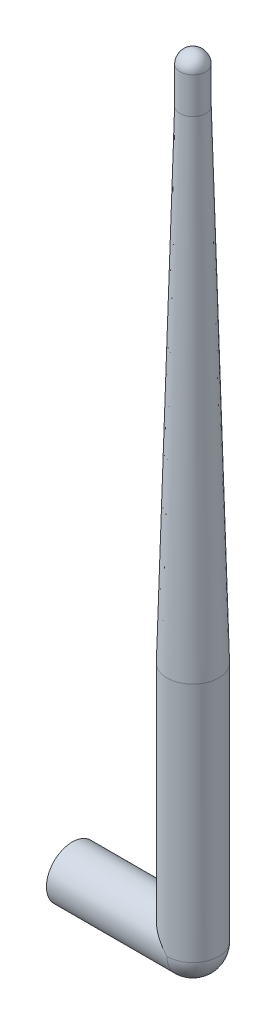
SolidWorks part; units mm, degrees
material "Rubber"
ref_plane "Front Plane" through (0, 0, 0) normal (0, 0, 1) x (1, 0, 0)
ref_plane "Top Plane" through (0, 0, 0) normal (0, 1, 0) x (1, 0, 0)
ref_plane "Right Plane" through (0, 0, 0) normal (1, 0, 0) x (0, 0, -1)
sketch "Sketch1" plane through (0, 0, 0) normal (1, 0, 0) x (0, 0, -1)
  circle A0 centre (0, 0) radius 5.461
  dimension "D1" = 10.922
extrude "Boss-Extrude1" add sketch "Sketch1" along normal blind 25.4
sketch "Sketch2" plane through (0, 0, 0) normal (-1, 0, 0) x (0, 0, 1)
  circle A0 centre (0, 0) radius 4.191
  dimension "D1" = 8.382
extrude "Cut-Extrude1" cut sketch "Sketch2" against normal blind 7.62
sketch "Sketch3" plane through (0, 0, 0) normal (0, 1, 0) x (1, 0, 0)
  line L0 (25.4, -5.461) -> (25.4, 5.461) construction
  circle A0 centre (25.4, 0) radius 5.461
extrude "Boss-Extrude2" add sketch "Sketch3" along normal blind 50.8
sketch "Sketch7" plane through (25.4, 0, 0) normal (1, 0, 0) x (0, 0, -1)
  line L0 (5.461, 0) -> (-5.461, 0) construction
  line L1 (5.461, 0) -> (-5.461, 0)
  arc A0 (-5.461, 0) -> (5.461, 0) centre (0, 0) ccw construction
  arc A1 (-5.461, 0) -> (5.461, 0) centre (0, 0) ccw
revolve "Revolve2" add sketch "Sketch7" angle 90 about L1
ref_plane "Plane1" through (0, 152.4, 0) normal (0, 1, 0) x (1, 0, 0)
sketch "Sketch8" plane through (0, 152.4, 0) normal (0, 1, 0) x (1, 0, 0)
  circle A2 centre (25.4, 0) radius 2.7305
  arc A3 (25.4, 2.7305) -> (25.4, -2.7305) centre (25.4, 0) ccw
loft "Loft2" add section face at (25.4, 50.8, 5.461) section "Sketch8"
sketch "Sketch9" plane through (0, 152.4, 0) normal (0, 1, 0) x (1, 0, 0)
  circle A0 centre (25.4, 0) radius 2.7305
extrude "Boss-Extrude3" add sketch "Sketch9" along normal blind 7.62
sketch "Sketch10" plane through (0, 160.02, 0) normal (0, 1, 0) x (1, 0, 0)
  line L0 (25.4, 2.7305) -> (25.4, -2.7305)
  arc A0 (25.4, -2.7305) -> (25.4, 2.7305) centre (25.4, 0) ccw
revolve "Revolve3" add sketch "Sketch10" angle 180 about L0
